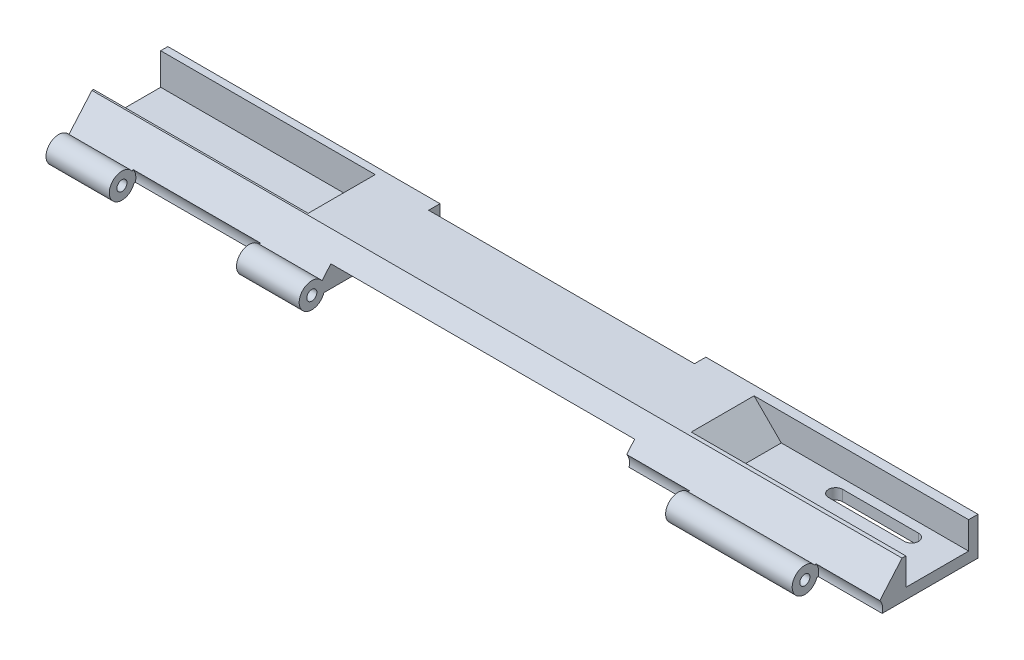
SolidWorks part; units mm, degrees
ref_plane "Front Plane" through (0, 0, 0) normal (0, 0, 1) x (1, 0, 0)
ref_plane "Top Plane" through (0, 0, 0) normal (0, 1, 0) x (1, 0, 0)
ref_plane "Right Plane" through (0, 0, 0) normal (1, 0, 0) x (0, 0, -1)
sketch "Sketch1" plane through (0, 0, 0) normal (1, 0, 0) x (0, 0, -1)
  line L5 (11.2654, -2.6366) -> (11.4585, -2.6366)
  line L6 (11.4585, -2.6366) -> (31.7785, -2.6366)
  line L7 (31.7785, -2.6366) -> (31.7785, 4.9834)
  line L8 (31.7785, 4.9834) -> (16.5385, 4.9834)
  line L9 (16.5385, 4.9834) -> (11.2654, -1.1126)
  circle A0 centre (9.8583, -1.8746) radius 0.8128
  circle A1 centre (9.8583, -1.8746) radius 1.6002
extrude "Boss-Extrude5" add sketch "Sketch1" along normal blind 162.56 contours A1 L5 L6 L7 L8 L9 | A1 A0
sketch "Sketch2" plane through (0, 0, -31.7785) normal (0, 0, -1) x (-1, 0, 0)
  line L0 (0, 4.9834) -> (0, -0.8586)
  line L1 (0, -2.6366) -> (0, 4.9834) construction
  line L2 (0, -0.8586) -> (-17.78, -0.8586)
  line L3 (-17.78, -0.8586) -> (-23.622, 4.9834)
  line L4 (-162.56, 4.9834) -> (0, 4.9834) construction
  line L5 (-23.622, 4.9834) -> (0, 4.9834)
extrude "Cut-Extrude1" cut sketch "Sketch2" against normal blind 14.351
sketch "Sketch3" plane through (0, 0, 0) normal (-1, 0, 0) x (0, 0, 1)
  line L0 (-31.7785, -0.8586) -> (-31.7785, 4.9834)
  line L1 (-31.7785, 4.9834) -> (-30.8895, 4.9834)
  line L2 (-17.4275, 4.9834) -> (-31.7785, 4.9834) construction
  line L3 (-30.8895, 4.9834) -> (-30.8895, -0.8586)
  line L4 (-17.4275, -0.8586) -> (-31.7785, -0.8586) construction
  line L5 (-30.8895, -0.8586) -> (-31.7785, -0.8586)
extrude "Boss-Extrude6" add sketch "Sketch3" against normal blind 36.957
sketch "Sketch7" plane through (0, 0, -31.7785) normal (0, 0, -1) x (-1, 0, 0)
  line L0 (-162.56, 4.9834) -> (-162.56, -0.4776)
  line L1 (-162.56, -2.6366) -> (-162.56, 4.9834) construction
  line L2 (-162.56, -0.4776) -> (-142.24, -0.4776)
  line L6 (-142.24, -0.4776) -> (-136.779, 4.9834)
  line L7 (-162.56, 4.9834) -> (0, 4.9834) construction
  line L8 (-136.779, 4.9834) -> (-162.56, 4.9834)
sketch "Sketch10" plane through (0, 0, -31.7785) normal (0, 0, -1) x (-1, 0, 0)
  line L0 (-162.56, -0.4776) -> (-142.24, -0.4776)
  line L1 (-142.24, -0.4776) -> (-136.779, 4.9834)
  line L2 (-136.779, 4.9834) -> (-162.56, 4.9834)
  line L3 (-162.56, 4.9834) -> (-162.56, -0.4776)
sketch "Sketch16" plane through (0, 0, 0) normal (-1, 0, 0) x (0, 0, 1)
  line L0 (-30.8895, 4.9834) -> (-17.4275, 4.9834)
  line L1 (-17.4275, 4.9834) -> (-17.4275, -1.4767)
  line L2 (-17.4275, -1.4767) -> (-30.8895, -1.4767)
  line L3 (-30.8895, -1.4767) -> (-30.8895, 4.9834)
extrude "Boss-Extrude7" add sketch "Sketch16" against normal blind 33.02
sketch "Sketch17" plane through (0, 0, -31.7785) normal (0, 0, -1) x (-1, 0, 0)
  line L0 (0, 4.9834) -> (0, -0.8586)
  line L1 (0, -2.6366) -> (0, 4.9834) construction
  line L2 (0, -0.8586) -> (-17.78, -0.8586)
  line L3 (-17.78, -0.8586) -> (-23.622, 4.9834)
  line L4 (-162.56, 4.9834) -> (0, 4.9834) construction
  line L5 (-23.622, 4.9834) -> (0, 4.9834)
extrude "Cut-Extrude4" cut sketch "Sketch17" against normal blind 15.24
sketch "Sketch18" plane through (0, 0, 0) normal (-1, 0, 0) x (0, 0, 1)
  line L0 (-31.7785, -0.8586) -> (-31.7785, 4.9834)
  line L1 (-31.7785, 4.9834) -> (-30.0005, 4.9834)
  line L2 (-16.5385, 4.9834) -> (-31.7785, 4.9834) construction
  line L3 (-30.0005, 4.9834) -> (-30.0005, -0.8586)
  line L4 (-16.5385, -0.8586) -> (-31.7785, -0.8586) construction
  line L5 (-30.0005, -0.8586) -> (-31.7785, -0.8586)
extrude "Boss-Extrude8" add sketch "Sketch18" against normal blind 38.1
sketch "Sketch19" plane through (0, 0, -31.7785) normal (0, 0, -1) x (-1, 0, 0)
  line L0 (-162.56, 4.9834) -> (-162.56, -0.4776)
  line L1 (-162.56, -0.4776) -> (-142.24, -0.4776)
  line L2 (-142.24, -0.4776) -> (-136.779, 4.9834)
  line L3 (-136.779, 4.9834) -> (-162.56, 4.9834)
extrude "Cut-Extrude5" cut sketch "Sketch19" against normal blind 14.224
sketch "Sketch20" plane through (162.56, 0, 0) normal (1, 0, 0) x (0, 0, -1)
  line L0 (31.7785, -0.4776) -> (31.7785, 4.9834)
  line L1 (31.7785, 4.9834) -> (29.6449, 4.9834)
  line L2 (17.5545, 4.9834) -> (31.7785, 4.9834) construction
  line L3 (29.6449, 4.9834) -> (29.6449, -0.4776)
  line L4 (17.5545, -0.4776) -> (31.7785, -0.4776) construction
  line L5 (29.6449, -0.4776) -> (31.7785, -0.4776)
extrude "Boss-Extrude9" add sketch "Sketch20" against normal blind 36.322
sketch "Sketch22" plane through (0, -0.4776, 0) normal (0, 1, 0) x (1, 0, 0)
  line L0 (157.2171, 21.9741) -> (145.9484, 21.9741)
  line L2 (157.2171, 19.1293) -> (145.9484, 19.1293)
  line L3 (145.9484, 25.1491) -> (157.2171, 25.1491)
  line L4 (145.9484, 27.9939) -> (157.2171, 27.9939)
  circle A0 centre (145.9484, 26.5715) radius 1.4224
  circle A1 centre (145.9484, 20.5517) radius 1.4224
  circle A2 centre (157.2171, 26.5715) radius 1.4224
  circle A3 centre (157.2171, 20.5517) radius 1.4224
extrude "Cut-Extrude7" cut sketch "Sketch22" against normal blind 24.13 and the other way blind 20.32 contours A0 | A2 L4 A0 L3 | A2 | A3 L0 A1 L2 | A3 | A1
sketch "Sketch25" plane through (0, 4.9834, 0) normal (0, 1, 0) x (1, 0, 0)
  line L0 (0, 11.2654) -> (0, 8.2581)
  line L1 (0, 8.2581) -> (25.146, 8.2581)
  line L2 (0, 8.2581) -> (162.56, 8.2581) construction
  line L3 (162.56, 8.2581) -> (137.414, 8.2581)
  line L4 (162.56, 8.2581) -> (162.56, 11.2654) construction
  line L5 (137.414, 8.2581) -> (137.414, 11.2654)
  line L6 (162.56, 11.2654) -> (0, 11.2654) construction
  line L7 (137.414, 11.2654) -> (25.146, 11.2654)
  line L8 (25.146, 11.2654) -> (25.146, 8.2581)
  line L9 (25.146, 8.2581) -> (137.414, 8.2581)
extrude "Cut-Extrude8" cut sketch "Sketch25" against normal blind 24.13 contours L8 L9 L5 L7
sketch "Sketch27" plane through (137.414, 0, 0) normal (-1, 0, 0) x (0, 0, 1)
  circle A0 centre (-9.8583, -1.8746) radius 1.778
extrude "Cut-Extrude9" cut sketch "Sketch27" along normal blind 112.268
sketch "Sketch31" plane through (0, 0, -31.7785) normal (0, 0, -1) x (-1, 0, 0)
  line L0 (-162.56, 4.9834) -> (-162.56, -0.4776)
  line L1 (-162.56, -2.6366) -> (-162.56, 4.9834) construction
  line L2 (-162.56, -0.4776) -> (-124.968, -0.4776)
  line L4 (-162.56, 4.9834) -> (0, 4.9834) construction
  line L5 (-124.079, 4.9834) -> (-162.56, 4.9834)
  line L6 (-124.968, -0.4776) -> (-119.507, 4.9834)
  line L7 (-119.507, 4.9834) -> (-124.079, 4.9834)
extrude "Cut-Extrude12" cut sketch "Sketch31" against normal blind 14.224
sketch "Sketch34" plane through (0, 4.9834, 0) normal (0, 1, 0) x (1, 0, 0)
  line L0 (119.507, 31.7785) -> (162.56, 31.7785)
  line L1 (162.56, 31.7785) -> (162.56, 29.6449)
  line L2 (162.56, 17.5545) -> (162.56, 31.7785) construction
  line L3 (162.56, 29.6449) -> (119.507, 29.6449)
  line L4 (119.507, 17.5545) -> (119.507, 31.7785) construction
  line L5 (119.507, 29.6449) -> (119.507, 31.7785)
extrude "Boss-Extrude14" add sketch "Sketch34" against normal blind 7.112
sketch "Sketch35" plane through (0, -0.4776, 0) normal (0, 1, 0) x (1, 0, 0)
  line L0 (162.56, 23.5997) -> (130.048, 23.5997)
  line L1 (162.56, 17.5545) -> (162.56, 29.6449) construction
  line L2 (145.9484, 25.1491) -> (130.048, 25.1491)
  line L3 (145.9484, 27.9939) -> (130.048, 27.9939)
  line L5 (145.9484, 21.9741) -> (130.048, 21.9741)
  line L6 (145.9484, 19.1293) -> (130.048, 19.1293)
  circle A0 centre (130.048, 26.5715) radius 1.4224
  circle A1 centre (130.048, 20.5517) radius 1.4224
  arc M2 (145.9484, 25.1491) -> (145.9484, 27.9939) centre (145.9484, 26.5715) cw
  arc M12 (145.9484, 19.1293) -> (145.9484, 21.9741) centre (145.9484, 20.5517) cw
extrude "Cut-Extrude13" cut sketch "Sketch35" against normal blind 7.112 contours A0 L2 L3 M2 | A1 L6 L5 M12 | A1 | A0
sketch "Sketch37" plane through (0, -2.6366, 0) normal (0, -1, 0) x (-1, 0, 0)
  line L3 (-111.76, 29.2385) -> (-111.76, 13.9985)
  line L4 (-111.76, 13.9985) -> (-50.8, 13.9985)
  line L5 (-50.8, 13.9985) -> (-50.8, 29.2385)
  line L6 (-50.8, 29.2385) -> (-111.76, 29.2385)
extrude "Cut-Extrude14" cut sketch "Sketch37" against normal blind 3.048
sketch "Sketch38" plane through (111.76, 0, 0) normal (-1, 0, 0) x (0, 0, 1)
  line L0 (-29.2385, -1.1126) -> (-27.9685, -1.1126)
  line L1 (-29.2385, 0.4114) -> (-29.2385, -2.6366) construction
  circle A0 centre (-27.9685, -1.1126) radius 0.8128
extrude "Cut-Extrude15" cut sketch "Sketch38" against normal blind 5.08
sketch "Sketch39" plane through (50.8, 0, 0) normal (1, 0, 0) x (0, 0, -1)
  line L0 (29.2385, -1.1126) -> (27.9685, -1.1126)
  line L1 (29.2385, 0.4114) -> (29.2385, -2.6366) construction
  circle A0 centre (27.9685, -1.1126) radius 0.8128
extrude "Cut-Extrude16" cut sketch "Sketch39" against normal blind 5.08
sketch "Sketch40" plane through (0, -2.6366, 0) normal (0, -1, 0) x (-1, 0, 0)
  line L0 (-111.76, 29.2385) -> (-111.76, 31.7785)
  line L1 (-162.56, 31.7785) -> (0, 31.7785) construction
  line L2 (-111.76, 31.7785) -> (-50.8, 31.7785)
  line L3 (-50.8, 31.7785) -> (-50.8, 29.2385)
  line L4 (-50.8, 29.2385) -> (-111.76, 29.2385)
extrude "Cut-Extrude17" cut sketch "Sketch40" against normal blind 3.048
sketch "Sketch41" plane through (50.8, 0, 0) normal (1, 0, 0) x (0, 0, -1)
  circle A0 centre (27.9685, -1.1126) radius 1.1613
extrude "Boss-Extrude15" add sketch "Sketch41" against normal blind 6.604
sketch "Sketch42" plane through (111.76, 0, 0) normal (-1, 0, 0) x (0, 0, 1)
  circle A0 centre (-27.9685, -1.1126) radius 1.0208
extrude "Boss-Extrude16" add sketch "Sketch42" against normal blind 5.588
sketch "Sketch43" plane through (50.8, 0, 0) normal (1, 0, 0) x (0, 0, -1)
  line L0 (31.7785, -1.1126) -> (30.5085, -1.1126)
  line L1 (31.7785, 0.4114) -> (31.7785, -2.6366) construction
  circle A0 centre (30.5085, -1.1126) radius 0.8128
extrude "Cut-Extrude18" cut sketch "Sketch43" against normal blind 5.08
sketch "Sketch44" plane through (111.76, 0, 0) normal (-1, 0, 0) x (0, 0, 1)
  line L0 (-31.7785, -1.1126) -> (-30.5085, -1.1126)
  line L1 (-31.7785, 0.4114) -> (-31.7785, -2.6366) construction
  circle A0 centre (-30.5085, -1.1126) radius 0.8128
extrude "Cut-Extrude19" cut sketch "Sketch44" against normal blind 5.08
sketch "Sketch46" plane through (0, -2.6366, 0) normal (0, -1, 0) x (-1, 0, 0)
  line L0 (-111.76, 13.9985) -> (-111.76, 4.9105)
  line L1 (-111.76, 4.9105) -> (-50.8, 4.9105)
  line L2 (-50.8, 4.9105) -> (-50.8, 13.9985)
  line L3 (-50.8, 13.9985) -> (-111.76, 13.9985)
extrude "Cut-Extrude21" cut sketch "Sketch46" against normal blind 3.048
sketch "Sketch47" plane through (0, 0.4114, 0) normal (0, -1, 0) x (-1, 0, 0)
  line L0 (-50.8, 31.7785) -> (-50.8, 29.4925)
  line L1 (-50.8, 11.4647) -> (-50.8, 31.7785) construction
  line L2 (-50.8, 29.4925) -> (-54.61, 29.4925)
  line L3 (-54.61, 29.4925) -> (-54.61, 31.7785)
  line L4 (-50.8, 31.7785) -> (-111.76, 31.7785) construction
  line L5 (-54.61, 31.7785) -> (-107.95, 31.7785)
  line L6 (-107.95, 31.7785) -> (-107.95, 29.4925)
  line L7 (-107.95, 29.4925) -> (-54.61, 29.4925)
  line M5 (-50.8, 31.7785) -> (-111.76, 31.7785)
extrude "Cut-Extrude22" cut sketch "Sketch47" against normal blind 15.24 contours L6 L7 L3 M5
sketch "Sketch48" plane through (0, 0, 0) normal (-1, 0, 0) x (0, 0, 1)
  circle A0 centre (-9.8583, -1.8746) radius 2.54
extrude "Boss-Extrude17" add sketch "Sketch48" against normal blind 25.146
sketch "Sketch49" plane through (162.56, 0, 0) normal (1, 0, 0) x (0, 0, -1)
  circle A0 centre (9.8583, -1.8746) radius 2.54
extrude "Boss-Extrude18" add sketch "Sketch49" against normal blind 25.146
sketch "Sketch50" plane through (137.414, 0, 0) normal (-1, 0, 0) x (0, 0, 1)
  circle A0 centre (-9.8583, -1.8746) radius 2.794
extrude "Cut-Extrude23" cut sketch "Sketch50" along normal blind 112.268
sketch "Sketch51" plane through (162.56, 0, 0) normal (1, 0, 0) x (0, 0, -1)
  circle A0 centre (9.8583, -1.8746) radius 1.27
extrude "Cut-Extrude24" cut sketch "Sketch51" against normal blind 174.498
sketch "Sketch52" plane through (0, 0.4114, 0) normal (0, -1, 0) x (-1, 0, 0)
  line L0 (-50.8, 31.7785) -> (-50.8, 12.5464)
  line L1 (-50.8, 12.5464) -> (-111.76, 12.6523)
  line L2 (-111.76, 12.6523) -> (-111.76, 31.7785)
  line L3 (-111.76, 31.7785) -> (-50.8, 31.7785)
extrude "Cut-Extrude25" cut sketch "Sketch52" against normal blind 1.27
ref_plane "Plane1" through (72.2732, 0.4114, -12.5837) normal (-1, 0, 0) x (0, 0, 1)
sketch "Sketch55" plane through (0, -2.6366, 0) normal (0, -1, 0) x (1, 0, 0)
  line L0 (111.76, -13.6822) -> (111.76, -7.8087)
  line L1 (111.76, -7.8087) -> (65.0565, -7.8087)
  line L2 (65.0565, -7.8087) -> (65.0565, -13.6822)
  line L3 (50.8, -13.6822) -> (111.76, -13.6822) construction
  line L4 (65.0565, -13.6822) -> (111.76, -13.6822)
extrude "Cut-Extrude26" cut sketch "Sketch55" against normal blind 8.636 and the other way blind 9.144
sketch "Sketch57" plane through (45.72, 0, 0) normal (1, 0, 0) x (0, 0, -1)
  circle A0 centre (30.5085, -1.1126) radius 1.0293
extrude "Boss-Extrude20" add sketch "Sketch57" along normal blind 5.08
sketch "Sketch58" plane through (111.76, 0, 0) normal (-1, 0, 0) x (0, 0, 1)
  circle A0 centre (-30.5085, -1.1126) radius 1.0927
extrude "Boss-Extrude21" add sketch "Sketch58" against normal blind 7.112
sketch "Sketch59" plane through (50.8, 0, 0) normal (1, 0, 0) x (0, 0, -1)
  line L0 (31.7785, -0.4776) -> (29.2385, -0.4776)
  line L1 (31.7785, 1.6814) -> (31.7785, -2.6366) construction
  circle A0 centre (29.2385, -0.4776) radius 1.016
extrude "Cut-Extrude27" cut sketch "Sketch59" against normal blind 5.08 and the other way blind 66.04
sketch "Sketch60" plane through (0, 0, 0) normal (-1, 0, 0) x (0, 0, 1)
  circle A0 centre (-9.8583, -1.8746) radius 1.016
  circle A1 centre (-9.8583, -1.8746) radius 1.8695
extrude "Boss-Extrude22" add sketch "Sketch60" against normal blind 162.56
sketch "Sketch61" plane through (137.414, 0, 0) normal (-1, 0, 0) x (0, 0, 1)
  circle A0 centre (-9.8583, -1.8746) radius 2.2194
extrude "Cut-Extrude28" cut sketch "Sketch61" along normal blind 112.268
sketch "Sketch62" plane through (25.146, 0, 0) normal (1, 0, 0) x (0, 0, -1)
  line L0 (11.9061, -0.3719) -> (12.4252, 0.2282)
  line L1 (12.2813, -2.6366) -> (12.6983, -2.6366)
  line L2 (12.6983, -2.6366) -> (12.8765, -1.4304)
  line L3 (12.4252, 0.2282) -> (12.8765, -1.4304)
  circle A0 centre (9.8583, -1.8746) radius 2.54
  circle A1 centre (9.8583, -1.8746) radius 1.016
  arc M1 (11.9061, -0.3719) -> (12.2813, -2.6366) centre (9.8583, -1.8746) ccw
  line M2 (12.2813, -2.6366) -> (12.5464, -2.6366)
  arc M3 (12.5464, -2.6366) -> (12.0761, -0.1753) centre (9.8583, -1.8746) ccw
  line M4 (12.0761, -0.1753) -> (11.9061, -0.3719)
  circle M5 centre (9.8583, -1.8746) radius 1.016
extrude "Boss-Extrude26" add sketch "Sketch62" along normal blind 25.654 contours A0 M2 M3 M4 | A0 M1 M5
sketch "Sketch65" plane through (137.414, 0, 0) normal (-1, 0, 0) x (0, 0, 1)
  line L0 (-11.9061, -0.3719) -> (-12.3768, 0.1722)
  line L1 (-12.2813, -2.6366) -> (-13.0464, -2.6366)
  line L2 (-13.0464, -2.6366) -> (-13.0464, -0.8123)
  line L3 (-13.0464, -0.8123) -> (-12.3768, 0.1722)
  circle A0 centre (-9.8583, -1.8746) radius 2.54
  circle A1 centre (-9.8583, -1.8746) radius 1.016
  line M1 (-12.5464, -2.6366) -> (-12.2813, -2.6366)
  arc M2 (-12.2813, -2.6366) -> (-11.9061, -0.3719) centre (-9.8583, -1.8746) ccw
  line M3 (-11.9061, -0.3719) -> (-12.0761, -0.1753)
  arc M4 (-12.0761, -0.1753) -> (-12.5464, -2.6366) centre (-9.8583, -1.8746) ccw
  circle M5 centre (-9.8583, -1.8746) radius 1.016
extrude "Boss-Extrude27" add sketch "Sketch65" along normal blind 25.654 contours A0 M3 M4 M1 | A0 M2 M5
sketch "Sketch67" plane through (162.56, 0, 0) normal (1, 0, 0) x (0, 0, -1)
  circle A0 centre (9.8583, -1.8746) radius 2.794
extrude "Cut-Extrude32" cut sketch "Sketch67" against normal blind 12.827
sketch "Sketch68" plane through (111.76, 0, 0) normal (-1, 0, 0) x (0, 0, 1)
  circle A0 centre (-9.8583, -1.8746) radius 2.794
extrude "Cut-Extrude33" cut sketch "Sketch68" against normal blind 12.827
sketch "Sketch70" plane through (0, -6.0502, -6.9944) normal (0, 0.6542, 0.7563) x (1, 0, 0)
  line L0 (0, 7.5078) -> (12.573, 7.5078)
  line L1 (0, 7.5078) -> (50.8, 7.5078) construction
ref_plane "Plane2" through (12.573, 0, 0) normal (-1, 0, 0) x (0, 0, 1)
sketch "Sketch72" plane through (12.573, 0, 0) normal (-1, 0, 0) x (0, 0, 1)
  circle A0 centre (-9.8583, -1.8746) radius 2.794
extrude "Cut-Extrude34" cut sketch "Sketch72" against normal blind 25.654
sketch "Sketch74" plane through (12.573, 0, 0) normal (-1, 0, 0) x (0, 0, 1)
  line L0 (-12.2813, -2.6366) -> (-13.0347, -2.6366)
  line L1 (-12.5464, -2.6366) -> (-31.7785, -2.6366) construction
  line L2 (-13.0347, -2.6366) -> (-13.4092, -1.2331)
  line L3 (-13.4092, -1.2331) -> (-12.2813, 0.0618)
  line L4 (-16.5385, 4.9834) -> (-12.0761, -0.1753) construction
  line L5 (-12.2813, 0.0618) -> (-11.9061, -0.3719)
  circle A0 centre (-9.8583, -1.8746) radius 2.54
  circle A1 centre (-9.8583, -1.8746) radius 1.016
extrude "Boss-Extrude28" add sketch "Sketch74" against normal blind 0.127 contours A0 A1 | A0 L5 L3 L2 L0
sketch "Sketch77" plane through (124.587, 0, 0) normal (-1, 0, 0) x (0, 0, 1)
  line L0 (-12.2813, -2.6366) -> (-13.3172, -2.6366)
  line L1 (-12.5464, -2.6366) -> (-31.7785, -2.6366) construction
  line L2 (-13.3172, -2.6366) -> (-13.5466, -0.8586)
  line L3 (-13.5466, -0.8586) -> (-12.4857, 0.2981)
  line L4 (-16.5385, 4.9834) -> (-12.0761, -0.1753) construction
  line L5 (-12.4857, 0.2981) -> (-11.9061, -0.3719)
  circle A0 centre (-9.8583, -1.8746) radius 2.54
  circle A1 centre (-9.8583, -1.8746) radius 1.016
  line M1 (-11.9061, -0.3719) -> (-12.0761, -0.1753)
  arc M2 (-12.0761, -0.1753) -> (-12.5464, -2.6366) centre (-9.8583, -1.8746) ccw
  line M3 (-12.5464, -2.6366) -> (-12.2813, -2.6366)
  arc M4 (-12.2813, -2.6366) -> (-11.9061, -0.3719) centre (-9.8583, -1.8746) ccw
  circle M5 centre (-9.8583, -1.8746) radius 1.016
extrude "Boss-Extrude29" add sketch "Sketch77" along normal blind 0.254 contours A0 M4 M5 | A0 M1 M2 M3
sketch "Sketch79" plane through (0, 0, 0) normal (-1, 0, 0) x (0, 0, 1)
  circle A0 centre (-9.8583, -1.8746) radius 1.016
extrude "Cut-Extrude35" cut sketch "Sketch79" against normal blind 15.748
sketch "Sketch87" plane through (0, 4.9834, 0) normal (0, 1, 0) x (1, 0, 0)
  line L0 (23.622, 30.0005) -> (23.622, 16.5385)
  line L1 (23.622, 16.5385) -> (0, 16.5385)
  line L2 (0, 16.5385) -> (0, 30.0005)
  line L3 (0, 30.0005) -> (23.622, 30.0005)
extrude "Boss-Extrude30" add sketch "Sketch87" against normal blind 6.096
sketch "Sketch88" plane through (0, 0, -31.7785) normal (0, 0, -1) x (-1, 0, 0)
  line L0 (0, 4.9834) -> (0, -1.3666)
  line L1 (0, -2.6366) -> (0, 4.9834) construction
  line L2 (0, -1.3666) -> (-17.78, -1.3666)
  line L3 (0, 4.9834) -> (-23.622, 4.9834)
  line L4 (-54.61, 4.9834) -> (0, 4.9834) construction
  line L5 (-23.622, 4.9834) -> (-17.78, -1.3666)
extrude "Cut-Extrude36" cut sketch "Sketch88" against normal blind 14.9098
sketch "Sketch89" plane through (0, 0, 0) normal (-1, 0, 0) x (0, 0, 1)
  line L0 (-31.7785, -1.3666) -> (-31.7785, 4.9834)
  line L1 (-31.7785, 4.9834) -> (-30.3307, 4.9834)
  line L2 (-16.8687, 4.9834) -> (-31.7785, 4.9834) construction
  line L3 (-30.3307, 4.9834) -> (-30.3307, -1.3666)
  line L4 (-16.8687, -1.3666) -> (-31.7785, -1.3666) construction
  line L5 (-30.3307, -1.3666) -> (-31.7785, -1.3666)
extrude "Boss-Extrude31" add sketch "Sketch89" against normal blind 30.6578
sketch "Sketch90" plane through (0, -2.6366, 0) normal (0, -1, 0) x (-1, 0, 0)
  line L0 (-162.56, 23.2375) -> (-137.16, 23.2375)
  line L3 (-162.56, 12.5464) -> (-162.56, 31.7785) construction
  line L4 (-137.16, 27.9939) -> (-137.16, 30.1046)
  line L8 (-157.2171, 27.9939) -> (-130.048, 27.9939) construction
  line L9 (-137.16, 27.9939) -> (-137.16, 26.5715)
  line L10 (-130.048, 19.1293) -> (-157.2171, 19.1293) construction
  line L11 (-137.16, 19.1293) -> (-137.16, 20.5517)
  line L12 (-137.16, 30.1046) -> (-124.3834, 30.1046)
  line L13 (-124.3834, 30.1046) -> (-124.3834, 16.4483)
  line L14 (-124.3834, 16.4483) -> (-137.16, 16.4483)
  line L15 (-137.16, 16.4483) -> (-137.16, 19.1293)
  circle A0 centre (-137.16, 20.5517) radius 1.4224
  circle A1 centre (-137.16, 26.5715) radius 1.4224
  line M11 (-157.2171, 21.9741) -> (-130.048, 21.9741)
  arc M12 (-130.048, 21.9741) -> (-130.048, 19.1293) centre (-130.048, 20.5517) cw
  line M13 (-130.048, 19.1293) -> (-157.2171, 19.1293)
  line M15 (-157.2171, 27.9939) -> (-130.048, 27.9939)
  arc M16 (-130.048, 27.9939) -> (-130.048, 25.1491) centre (-130.048, 26.5715) cw
  line M17 (-130.048, 25.1491) -> (-157.2171, 25.1491)
extrude "Boss-Extrude32" add sketch "Sketch90" against normal blind 2.159 contours A1 M17 M16 M15 | A0 M13 M12 M11
sketch "Sketch91" plane through (0, -2.6366, 0) normal (0, -1, 0) x (-1, 0, 0)
  line L0 (-158.6395, 20.5517) -> (-154.8295, 20.5517)
  line L1 (-158.6395, 26.5715) -> (-154.8295, 26.5715)
  arc A0 (-157.2171, 21.9741) -> (-157.2171, 19.1293) centre (-157.2171, 20.5517) ccw construction
  arc A1 (-157.2171, 27.9939) -> (-157.2171, 25.1491) centre (-157.2171, 26.5715) ccw construction
  circle A2 centre (-154.8295, 26.5715) radius 1.4224
  circle A3 centre (-154.8295, 20.5517) radius 1.4224
  line M3 (-137.16, 19.1293) -> (-157.2171, 19.1293)
  arc M4 (-157.2171, 19.1293) -> (-157.2171, 21.9741) centre (-157.2171, 20.5517) cw
  line M5 (-157.2171, 21.9741) -> (-137.16, 21.9741)
  line M7 (-137.16, 25.1491) -> (-157.2171, 25.1491)
  arc M8 (-157.2171, 25.1491) -> (-157.2171, 27.9939) centre (-157.2171, 26.5715) cw
  line M9 (-157.2171, 27.9939) -> (-137.16, 27.9939)
extrude "Boss-Extrude33" add sketch "Sketch91" against normal blind 2.159 contours A2 L1 M8 M7 | A2 L1 M9 M8 | A3 L0 M5 M4 | A3 L0 M4 M3
sketch "Sketch92" plane through (162.56, 0, 0) normal (1, 0, 0) x (0, 0, -1)
  line L0 (29.6449, -0.4776) -> (29.8989, -0.4776)
  line L1 (29.8989, -0.4776) -> (29.8989, 4.9834)
  line L2 (29.6449, 4.9834) -> (31.7785, 4.9834) construction
  line L3 (29.8989, 4.9834) -> (17.3005, 4.9834)
  line L4 (17.5545, 4.9834) -> (16.5385, 4.9834) construction
  line L5 (17.3005, 4.9834) -> (17.3005, -0.4776)
  line L6 (17.3005, -0.4776) -> (29.6449, -0.4776)
extrude "Cut-Extrude38" cut sketch "Sketch92" against normal blind 43.053
sketch "Sketch94" plane through (0, 0, -31.7785) normal (0, 0, -1) x (-1, 0, 0)
  line L0 (-119.507, 4.9834) -> (-124.968, -0.4776)
  line L1 (-162.56, 4.9834) -> (-107.95, 4.9834) construction
  line L4 (-124.968, -0.4776) -> (-119.507, -0.4776)
  line L5 (-119.507, -0.4776) -> (-119.507, 4.9834)
extrude "Boss-Extrude35" add sketch "Sketch94" against normal blind 14.859
ref_plane "Plane4" through (23.622, 0, 0) normal (-1, 0, 0) x (0, 0, 1)
sketch "Sketch98" plane through (23.622, 0, 0) normal (-1, 0, 0) x (0, 0, 1)
  line L1 (-30.3307, -1.3666) -> (-16.8687, -1.3666)
  line L2 (-30.3307, -1.3666) -> (-30.3307, 4.9834)
  line L3 (-30.3307, 4.9834) -> (-16.8687, 4.9834)
  line L4 (-16.8687, -1.3666) -> (-16.8687, 4.9834)
extrude "Cut-Extrude41" cut sketch "Sketch98" against normal blind 19.431
sketch "Sketch101" plane through (0, 0, -31.7785) normal (0, 0, -1) x (-1, 0, 0)
  line L0 (-43.053, 4.9834) -> (-37.592, -0.4776)
  line L1 (-54.61, 4.9834) -> (0, 4.9834) construction
  line L3 (-37.592, -0.4776) -> (-43.053, -0.4776)
  line L4 (-43.053, -0.4776) -> (-43.053, 4.9834)
extrude "Boss-Extrude36" add sketch "Sketch101" against normal blind 15.113
sketch "Sketch102" plane through (0, 0, 0) normal (-1, 0, 0) x (0, 0, 1)
  line L1 (-30.3307, -1.3666) -> (-16.8687, -1.3666)
  line L2 (-30.3307, -1.3666) -> (-30.3307, 4.9834)
  line L3 (-30.3307, 4.9834) -> (-16.8687, 4.9834)
  line L4 (-16.8687, -1.3666) -> (-16.8687, 4.9834)
extrude "Cut-Extrude42" cut sketch "Sketch102" against normal blind 27.051
sketch "Sketch103" plane through (0, -0.4776, 0) normal (0, 1, 0) x (1, 0, 0)
  line L0 (137.16, 26.5715) -> (139.192, 26.5715)
  line L1 (137.16, 20.5517) -> (139.192, 20.5517)
  circle A0 centre (139.192, 26.5715) radius 1.4224
  circle A1 centre (139.192, 20.5517) radius 1.4224
extrude "Boss-Extrude39" add sketch "Sketch103" against normal blind 2.159
sketch "Sketch105" plane through (0, 0, -31.7785) normal (0, 0, -1) x (-1, 0, 0)
  line L0 (0, 4.9834) -> (-43.053, 4.9834)
  line L1 (-54.61, 4.9834) -> (0, 4.9834) construction
  line L2 (-43.053, 4.9834) -> (-35.8688, -2.2008)
  line L3 (-43.053, 4.9834) -> (-43.053, -2.2008)
  line L4 (-43.053, -2.2008) -> (-35.8688, -2.2008)
extrude "Boss-Extrude40" add sketch "Sketch105" against normal blind 14.986 contours L3 L4 L2
sketch "Sketch106" plane through (0, -0.4776, 0) normal (0, 1, 0) x (1, 0, 0)
  line L0 (139.192, 26.5715) -> (154.432, 26.5715)
  line L1 (139.192, 20.5517) -> (154.432, 20.5517)
  circle A0 centre (154.432, 26.5715) radius 1.4224
  circle A1 centre (154.432, 20.5517) radius 1.4224
  line M3 (139.192, 21.9741) -> (154.8295, 21.9741)
  arc M4 (154.8295, 21.9741) -> (154.8295, 19.1293) centre (154.8295, 20.5517) cw
  line M5 (154.8295, 19.1293) -> (139.192, 19.1293)
  line M6 (154.8295, 25.1491) -> (139.192, 25.1491)
  line M8 (139.192, 27.9939) -> (154.8295, 27.9939)
  arc M9 (154.8295, 27.9939) -> (154.8295, 25.1491) centre (154.8295, 26.5715) cw
extrude "Boss-Extrude41" add sketch "Sketch106" against normal blind 2.159 contours A0 M6 M9 M8 | A1 M5 M4 M3
